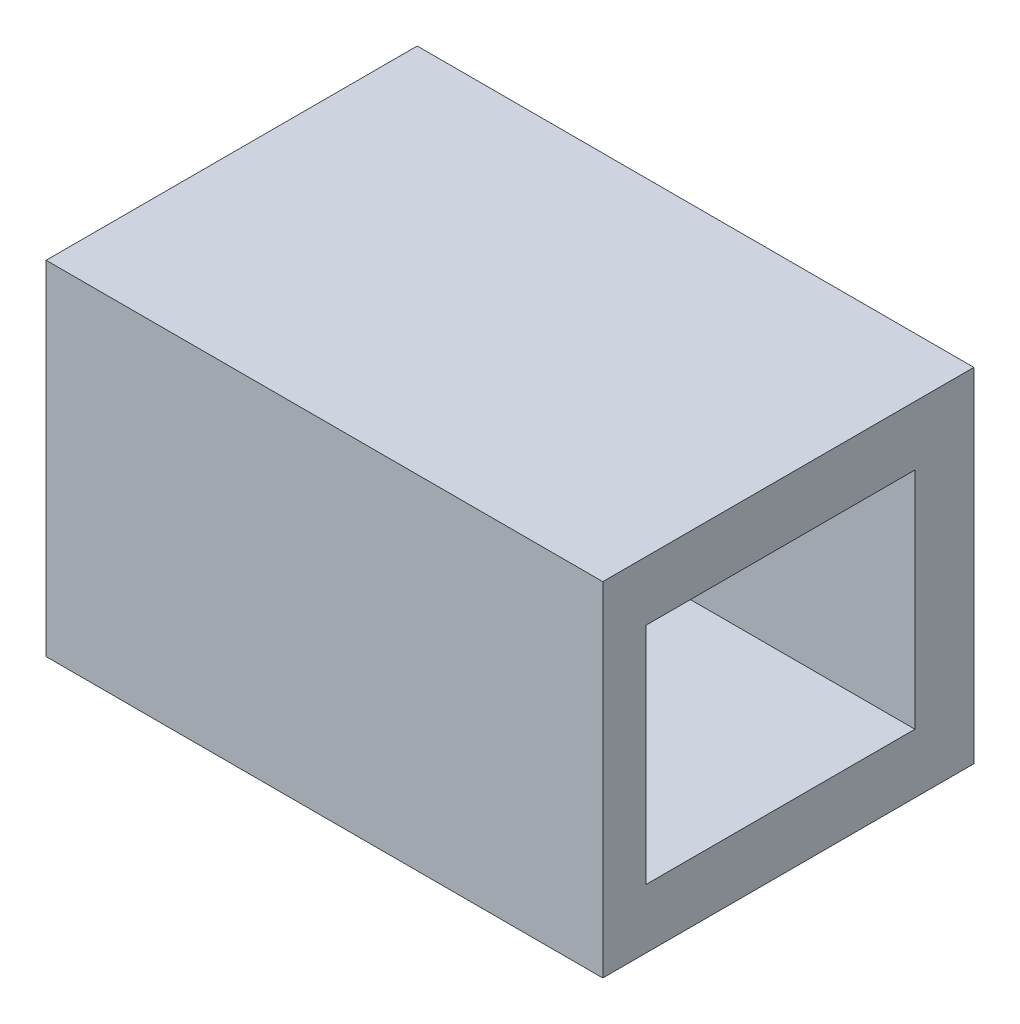
SolidWorks part; units mm, degrees
ref_plane "Plan de face" through (0, 0, 0) normal (0, 0, 1) x (1, 0, 0)
ref_plane "Plan de dessus" through (0, 0, 0) normal (0, 1, 0) x (1, 0, 0)
ref_plane "Plan de droite" through (0, 0, 0) normal (1, 0, 0) x (0, 0, -1)
sketch "Esquisse1" plane through (0, 0, 0) normal (0, 0, 1) x (1, 0, 0)
  line L1 (0, 0) -> (30, 0)
  line L2 (0, 0) -> (0, 18.5)
  line L3 (0, 18.5) -> (30, 18.5)
  line L4 (30, 0) -> (30, 18.5)
  dimension "D1" = 18.5
  dimension "D2" = 30
extrude "Boss.-Extru.1" add sketch "Esquisse1" along normal blind 20
sketch "Esquisse2" plane through (30, 0, 0) normal (1, 0, 0) x (0, 0, -1)
  line L0 (-20, 9.25) -> (0, 9.25) construction
  line L1 (-20, 0) -> (-20, 18.5) construction
  line L2 (0, 0) -> (0, 18.5) construction
  line L3 (-20, 3.2) -> (0, 3.2) construction
  line L4 (-20, 15.3) -> (0, 15.3) construction
  line L5 (-3.177, 0) -> (-3.177, 18.5) construction
  line L6 (-20, 0) -> (0, 0) construction
  line L7 (-20, 18.5) -> (0, 18.5) construction
  line L8 (-17.677, 0) -> (-17.677, 18.5) construction
  line L9 (-17.677, 3.2) -> (-17.677, 15.3)
  line L10 (-17.677, 15.3) -> (-3.177, 15.3)
  line L11 (-3.177, 15.3) -> (-3.177, 3.2)
  line L12 (-3.177, 3.2) -> (-17.677, 3.2)
  dimension "D1" = 6.05
  dimension "D2" = 14.5
extrude "Enlèv. mat.-Extru.1" cut sketch "Esquisse2" against normal blind 39
sketch "Esquisse3" plane through (0, 0, 20) normal (0, 0, 1) x (1, 0, 0)
  line L0 (5.318, 0) -> (5.318, 18.5) construction
  line L1 (0, 0) -> (30, 0) construction
  line L2 (30, 18.5) -> (0, 18.5) construction
  line L3 (22.418, 0) -> (22.418, 18.5) construction
  line L4 (30, 9.25) -> (0, 9.25) construction
  line L5 (30, 0) -> (30, 18.5) construction
  line L6 (0, 18.5) -> (0, 0) construction
  line L7 (30, 13.3776) -> (0, 13.3776) construction
  dimension "D1" = 17.1
